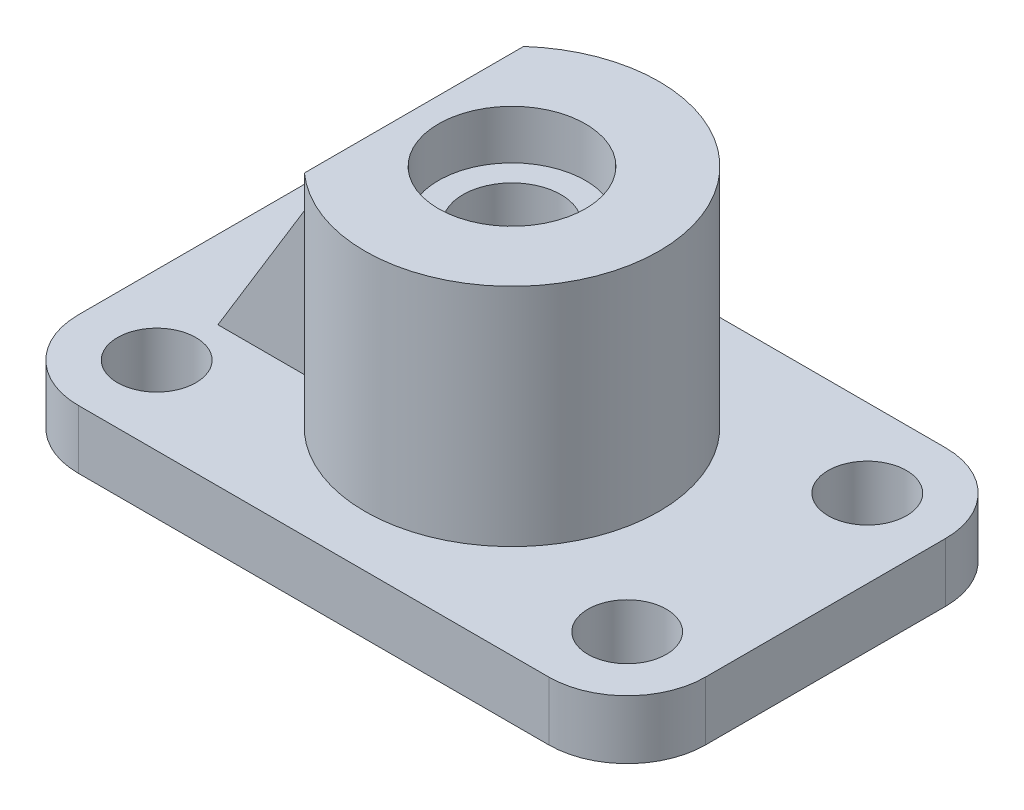
SolidWorks part; units mm, degrees
ref_plane "Ön Düzlem" through (0, 0, 0) normal (0, 0, 1) x (1, 0, 0)
ref_plane "Üst Düzlem" through (0, 0, 0) normal (0, 1, 0) x (1, 0, 0)
ref_plane "Sağ Düzlem" through (0, 0, 0) normal (1, 0, 0) x (0, 0, -1)
sketch "Çizim1" plane through (0, 0, 0) normal (0, 1, 0) x (1, 0, 0)
  line L0 (48, 0) -> (-48, 0)
  line L5 (64, 16) -> (64, 49)
  line L6 (-48, 81) -> (48, 81)
  line L7 (64, 49) -> (64, 65)
  line L8 (0, 0) -> (0, 81) construction
  line L9 (-64, 16) -> (-64, 49)
  line L10 (-64, 49) -> (-64, 65)
  arc A0 (-48, 0) -> (-64, 16) centre (-48, 16) cw
  arc A1 (-64, 65) -> (-48, 81) centre (-48, 65) cw
  arc A2 (48, 0) -> (64, 16) centre (48, 16) ccw
  arc A3 (64, 65) -> (48, 81) centre (48, 65) ccw
  circle A4 centre (-48, 65) radius 8
  circle A5 centre (-48, 16) radius 8
  circle A6 centre (48, 65) radius 8
  circle A7 centre (48, 16) radius 8
  dimension "D8" = 16
  dimension "D3" = 16
  dimension "D2" = 16
  dimension "D4" = 16
  dimension "D6" = 16
  dimension "D9" = 16
  dimension "D1" = 96
  dimension "D5" = 33
  dimension "D7" = 16
extrude "Yükseklik-Ekstrüzyon1" add sketch "Çizim1" along normal blind 12
sketch "Çizim2" plane through (0, 12, 0) normal (0, 1, 0) x (1, 0, 0)
  line L0 (-64, 65) -> (-64, 16) construction
  line L1 (0, 40.5) -> (-20, 40.5)
  line L2 (-20, 40.5) -> (-20, 62.8607)
  line L3 (-20, 40.5) -> (-20, 18.1393)
  arc A0 (-20, 18.1393) -> (-20, 62.8607) centre (0, 40.5) ccw
  circle A2 centre (0, 40.5) radius 15
  circle A3 centre (0, 40.5) radius 10
  dimension "D2" = 60
  dimension "D4" = 30
  dimension "D5" = 20
  dimension "D1" = 64
  dimension "D3" = 40.5
  dimension "D6" = 20
extrude "Yükseklik-Ekstrüzyon2" add sketch "Çizim2" along normal blind 46
sketch "Çizim4" plane through (0, 58, 0) normal (0, 1, 0) x (1, 0, 0)
  circle A1 centre (0, 40.5) radius 15
  dimension "D1" = 30
extrude "Kes-Ekstrüzyon1" cut sketch "Çizim4" against normal blind 10
sketch "Çizim5" plane through (0, 48, 0) normal (0, 1, 0) x (1, 0, 0)
  circle A0 centre (0, 40.5) radius 10
  dimension "D1" = 20
extrude "Kes-Ekstrüzyon2" cut sketch "Çizim5" against normal through all
ref_plane "Düzlem2" through (0, 0, -32.5) normal (0, 0, 1) x (1, 0, 0)
sketch "Çizim16" plane through (0, 0, -32.5) normal (0, 0, 1) x (1, 0, 0)
  line L0 (-48, 12) -> (-20, 58)
rib "Feder7" sketch "Çizim16" sketch "Çizim16" thickness 8 extrusion direction parallel to sketch draft on no parameters "D1"=8
